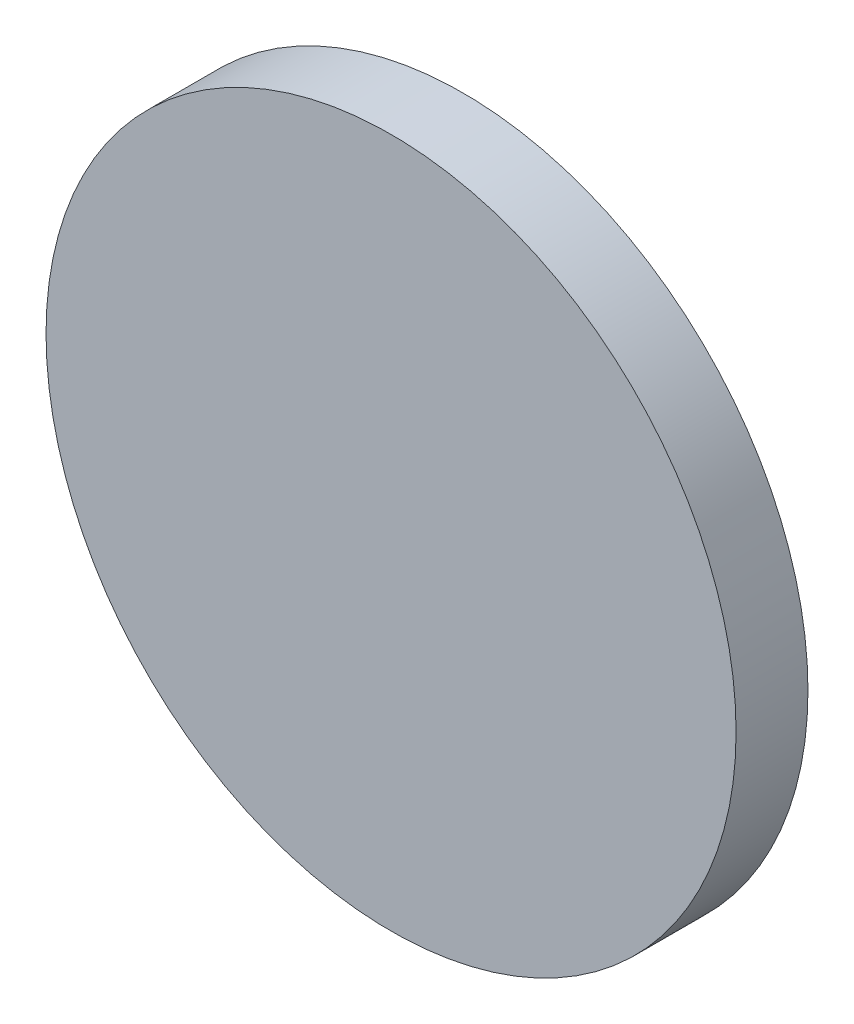
SolidWorks part; units mm, degrees
ref_plane "Front Plane" through (0, 0, 0) normal (0, 0, 1) x (1, 0, 0)
ref_plane "Top Plane" through (0, 0, 0) normal (0, 1, 0) x (1, 0, 0)
ref_plane "Right Plane" through (0, 0, 0) normal (1, 0, 0) x (0, 0, -1)
sketch "Sketch1" plane through (0, 0, 0) normal (0, 0, 1) x (1, 0, 0)
  circle A0 centre (0, 0) radius 240
extrude "Boss-Extrude1" add sketch "Sketch1" along normal blind 50
